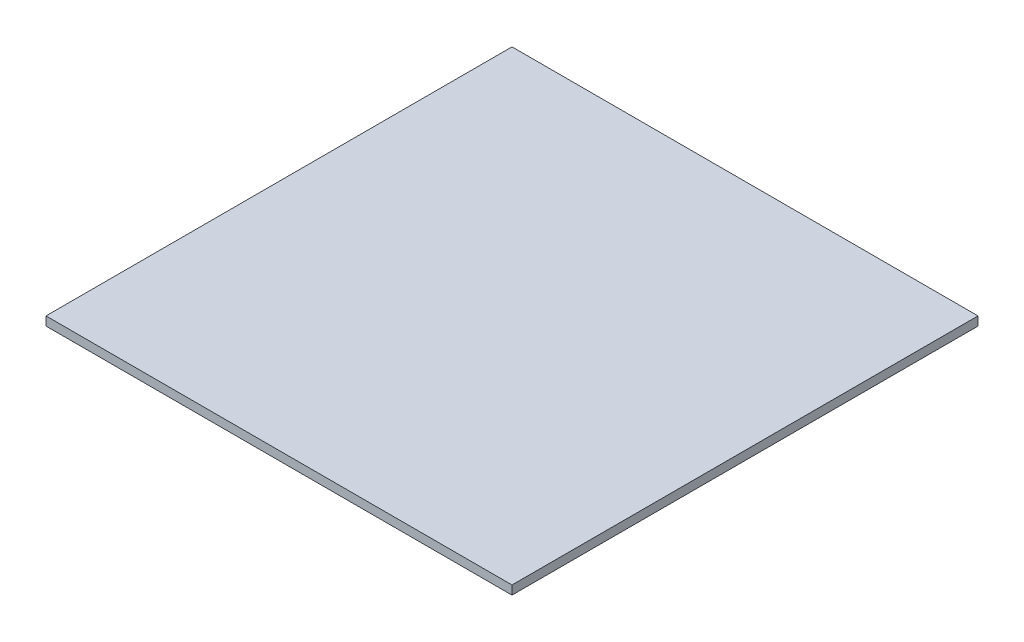
SolidWorks part; units mm, degrees
material "6061 Alloy"
ref_plane "Front" through (0, 0, 0) normal (0, 0, 1) x (1, 0, 0)
ref_plane "Top" through (0, 0, 0) normal (0, 1, 0) x (1, 0, 0)
ref_plane "Right" through (0, 0, 0) normal (1, 0, 0) x (0, 0, -1)
sketch "Sketch1" plane through (0, 0, 0) normal (0, 1, 0) x (1, 0, 0)
  line L1 (0, 0) -> (-108.585, 0)
  line L2 (0, 0) -> (0, 108.585)
  line L3 (0, 108.585) -> (-108.585, 108.585)
  line L4 (-108.585, 0) -> (-108.585, 108.585)
  dimension "D1" = 108.585
  dimension "D2" = 108.585
extrude "Main Plate" add sketch "Sketch1" along normal blind 1.5875
sketch "Sketch2" plane through (0, 1.5875, 0) normal (0, 1, 0) x (1, 0, 0)
  line L0 (-108.585, 0) -> (0, 0) construction
  line L1 (-121.285, 121.285) -> (12.7, 121.285)
  line L2 (-121.285, 121.285) -> (-121.285, -12.7)
  line L3 (-121.285, -12.7) -> (12.7, -12.7)
  line L4 (12.7, 121.285) -> (12.7, -12.7)
  line L5 (0, 108.585) -> (-108.585, 108.585) construction
  line L6 (-108.585, 108.585) -> (-108.585, 0) construction
  line L7 (0, 0) -> (0, 108.585) construction
  dimension "D1" = 12.7
  dimension "D2" = 12.7
  dimension "D3" = 12.7
  dimension "D4" = 12.7
extrude "Boss-Extrude2" add sketch "Sketch2" along normal blind 2.54
